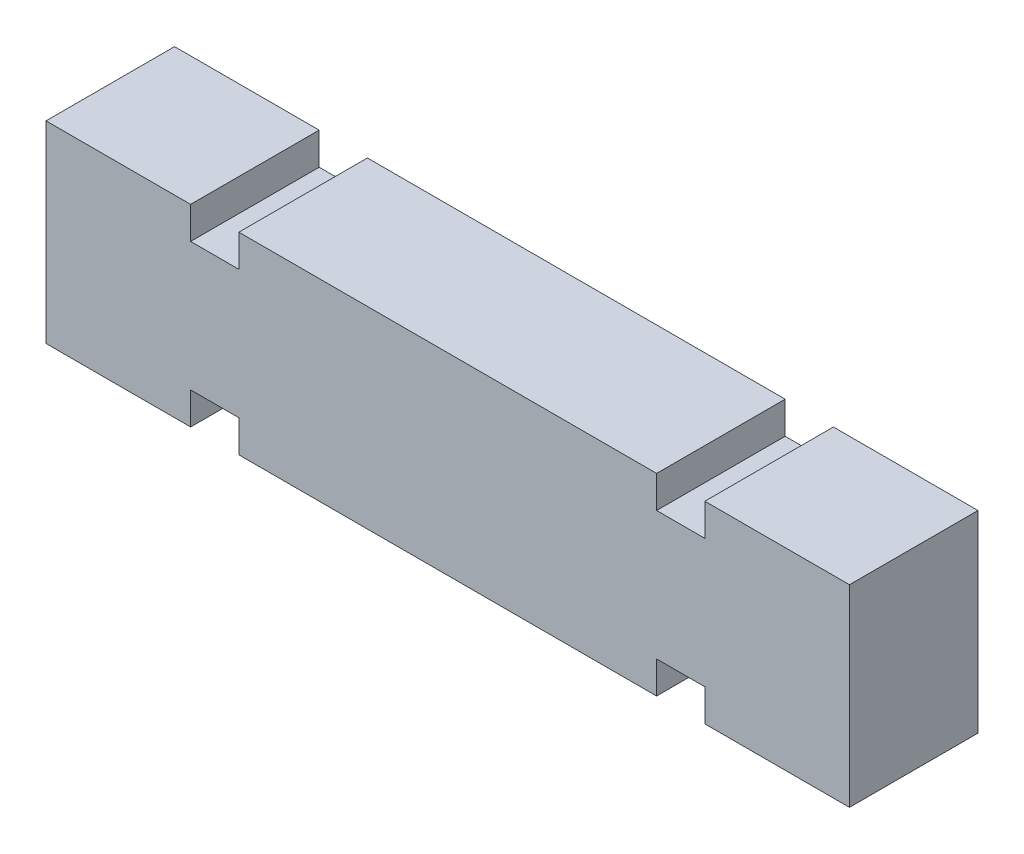
SolidWorks part; units mm, degrees
ref_plane "前视基准面" through (0, 0, 0) normal (0, 0, 1) x (1, 0, 0)
ref_plane "上视基准面" through (0, 0, 0) normal (0, 1, 0) x (1, 0, 0)
ref_plane "右视基准面" through (0, 0, 0) normal (1, 0, 0) x (0, 0, -1)
sketch "草图1" plane through (0, 0, 0) normal (1, 0, 0) x (0, 0, -1)
  line L1 (-2, 6) -> (2, 6)
  line L2 (2, 6) -> (2, 0)
  line L3 (2, 0) -> (-2, 0)
  line L4 (-2, 6) -> (-2, 0)
extrude "凸台-拉伸1" add sketch "草图1" along normal blind 25
sketch "草图3" plane through (0, 0, 0) normal (0, 0, 1) x (1, 0, 0)
  line L1 (4.5, 0) -> (6, 0)
  line L2 (6, 0) -> (6, 1)
  line L3 (6, 1) -> (4.5, 1)
  line L4 (4.5, 1) -> (4.5, 0)
  line L7 (0, 6) -> (0, 0) construction
  line L8 (4.5, 6) -> (6, 6)
  line L9 (6, 6) -> (6, 5)
  line L10 (6, 5) -> (4.5, 5)
  line L11 (4.5, 5) -> (4.5, 6)
  line L12 (20.5, 5) -> (20.5, 6)
  line L13 (20.5, 6) -> (19, 6)
  line L14 (19, 6) -> (19, 5)
  line L15 (19, 5) -> (20.5, 5)
  line L16 (19, 1) -> (20.5, 1)
  line L17 (20.5, 1) -> (20.5, 0)
  line L18 (20.5, 0) -> (19, 0)
  line L19 (19, 0) -> (19, 1)
  dimension "D1" = 1
  dimension "D2" = 1
  dimension "D3" = 1.5
  dimension "D4" = 4.5
extrude "切除-拉伸1" cut sketch "草图3" against normal mid plane 20
